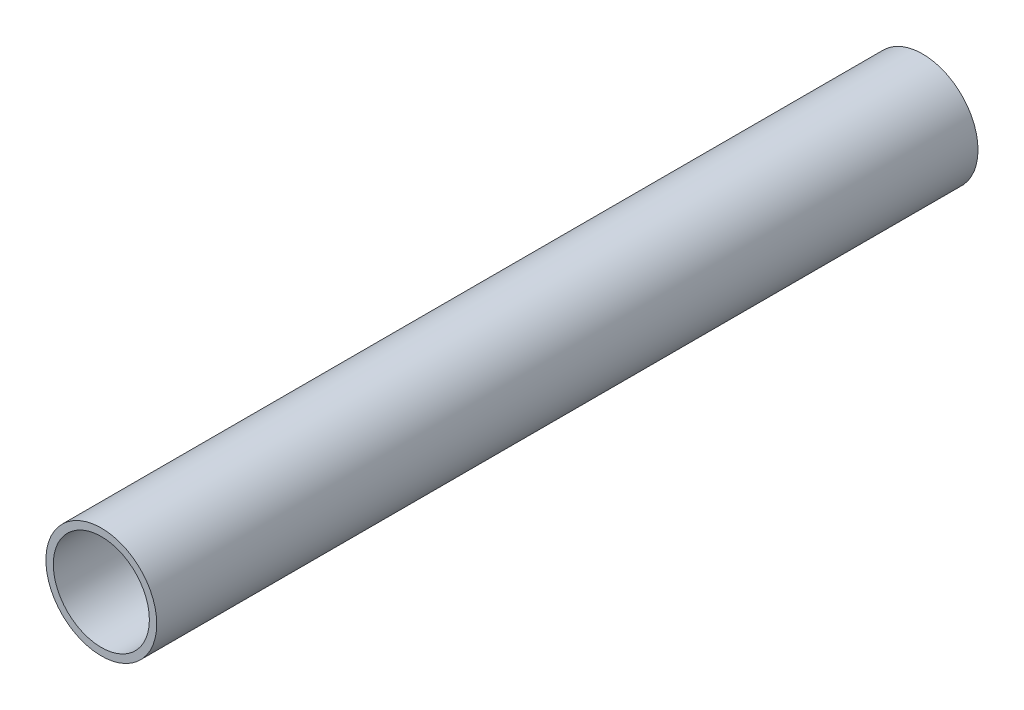
SolidWorks part; units mm, degrees
ref_plane "Front Plane" through (0, 0, 0) normal (0, 0, 1) x (1, 0, 0)
ref_plane "Top Plane" through (0, 0, 0) normal (0, 1, 0) x (1, 0, 0)
ref_plane "Right Plane" through (0, 0, 0) normal (1, 0, 0) x (0, 0, -1)
sketch "Sketch1" plane through (0, 0, 0) normal (0, 0, 1) x (1, 0, 0)
  circle A0 centre (0, 0) radius 13.5
  circle A1 centre (0, 0) radius 11.7
  dimension "D1" = 27
  dimension "D2" = 1.8
extrude "Boss-Extrude1" add sketch "Sketch1" along normal blind 200
